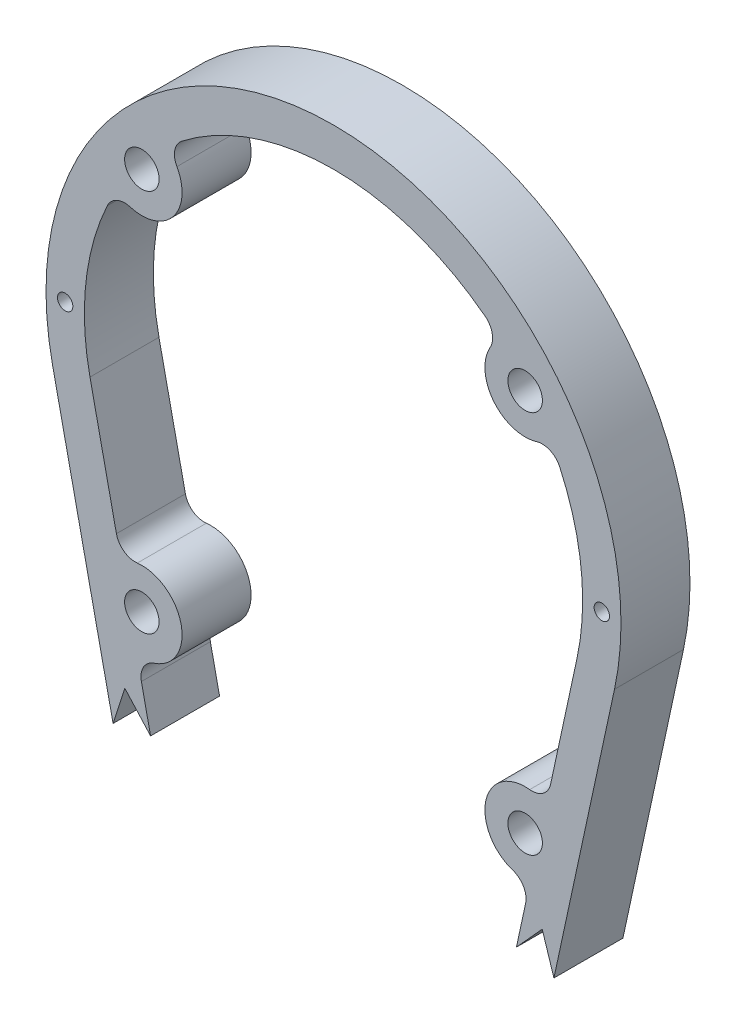
SolidWorks part; units mm, degrees
ref_plane "Front Plane" through (0, 0, 0) normal (0, 0, 1) x (1, 0, 0)
ref_plane "Top Plane" through (0, 0, 0) normal (0, 1, 0) x (1, 0, 0)
ref_plane "Right Plane" through (0, 0, 0) normal (1, 0, 0) x (0, 0, -1)
sketch "Sketch3" plane through (0, 0, 0) normal (0, 0, 1) x (1, 0, 0)
  line L0 (-31.9299, -122.5) -> (31.9299, -122.5)
  line L1 (41.7043, -114.6119) -> (73.3084, 31.6608)
  line L2 (-73.3084, 31.6608) -> (-41.7043, -114.6119)
  line L3 (-31.9299, -112.5) -> (-51.2845, -22.9211)
  line L4 (31.9299, -112.5) -> (51.2845, -22.9211)
  line L5 (-31.9299, -112.5) -> (31.9299, -112.5)
  line L6 (-55.4723, -3.5388) -> (-63.5339, 33.7727)
  line L8 (55.4723, -3.5388) -> (63.5339, 33.7727)
  arc A0 (31.9299, -122.5) -> (41.7043, -114.6119) centre (31.9299, -112.5) ccw
  arc A1 (73.3084, 31.6608) -> (-73.3084, 31.6608) centre (0, 47.5) ccw
  arc A2 (-41.7043, -114.6119) -> (-31.9299, -122.5) centre (-31.9299, -112.5) ccw
  circle A3 centre (50, -12.5) radius 4.5
  circle A4 centre (50, 87.5) radius 4.5
  circle A5 centre (-50, 87.5) radius 4.5
  circle A6 centre (-50, -12.5) radius 4.5
  arc A7 (63.5339, 33.7727) -> (56.6488, 79.3733) centre (0, 47.5) ccw
  arc A8 (-56.6488, 79.3733) -> (-43.531, 95.7706) centre (-50, 87.5) ccw
  arc A9 (43.531, 95.7706) -> (56.6488, 79.3733) centre (50, 87.5) ccw
  arc A10 (55.4723, -3.5388) -> (51.2845, -22.9211) centre (50, -12.5) ccw
  arc A11 (-51.2845, -22.9211) -> (-55.4723, -3.5388) centre (-50, -12.5) ccw
  arc A13 (43.531, 95.7706) -> (-43.531, 95.7706) centre (0, 47.5) ccw
  arc A15 (-56.6488, 79.3733) -> (-63.5339, 33.7727) centre (0, 47.5) ccw
  dimension "D1" = 10
  dimension "D2" = 6
  dimension "D3" = 10
  dimension "D4" = 10
  dimension "D5" = 10
  dimension "D6" = 6
  dimension "D7" = 6
  dimension "D8" = 6
extrude "Boss-Extrude1" add sketch "Sketch3" along normal blind 18
fillet "Fillet1" radius 5 2 edges at (31.9299, -112.5, 9) (-31.9299, -112.5, 9)
fillet "Fillet2" radius 5 8 edges at (-55.4723, -3.5388, 9) (55.4723, -3.5388, 9) (51.2845, -22.9211, 9) (-51.2845, -22.9211, 9) (56.6488, 79.3733, 9) (43.531, 95.7706, 9) (-43.531, 95.7706, 9) (-56.6488, 79.3733, 9)
sketch "Sketch5" plane through (0, 0, 18) normal (0, 0, 1) x (1, 0, 0)
  line L0 (0, 122.5) -> (106.1425, 122.5) construction
  line L1 (0, -122.5) -> (100.4685, -122.5) construction
  line L2 (-31.9299, -122.5) -> (31.9299, -122.5) construction
  line L3 (-47.7237, -39.4017) -> (0.048, -29.2744) construction
  line L4 (47.7244, -39.3984) -> (54.4443, -31.972)
  line L5 (-73.3084, 31.6608) -> (-41.7043, -114.6119) construction
  line L6 (0.048, -29.2744) -> (47.7244, -39.3984) construction
  line L7 (41.7043, -114.6119) -> (73.3084, 31.6608) construction
  line L8 (-57.5064, -41.4755) -> (-54.444, -31.9737)
  line L9 (-54.444, -31.9737) -> (-47.7237, -39.4017)
  line L10 (-50.1213, -28.305) -> (-32.782, -108.5559) construction
  line L11 (-47.7237, -39.4017) -> (47.7244, -39.3984)
  line L12 (32.782, -108.5559) -> (50.1213, -28.305) construction
  line L13 (54.4443, -31.972) -> (57.5064, -41.4755)
  line L14 (-57.5064, -41.4755) -> (-63.485, -126.0431)
  line L15 (-63.485, -126.0431) -> (70.3289, -126.0431)
  line L16 (70.3289, -126.0431) -> (57.5064, -41.4755)
  arc A0 (73.3084, 31.6608) -> (-73.3084, 31.6608) centre (0, 47.5) ccw construction
  dimension "D1" = 60
  dimension "D2" = 5
  dimension "D3" = 5
  dimension "D4" = 60
extrude "Cut-Extrude2" cut sketch "Sketch5" against normal through all
sketch "Sketch6" plane through (0, 0, 18) normal (0, 0, 1) x (1, 0, 0)
  line L0 (-75, 47.5) -> (75, 47.5) construction
  arc A0 (73.3084, 31.6608) -> (-73.3084, 31.6608) centre (0, 47.5) ccw construction
  circle A1 centre (-70, 47.5) radius 2
  circle A2 centre (70, 47.5) radius 2
  point P11 (0, 47.5)
  dimension "D1" = 4
  dimension "D2" = 4
  dimension "D3" = 70
  dimension "D4" = 70
extrude "Cut-Extrude3" cut sketch "Sketch6" against normal through all
